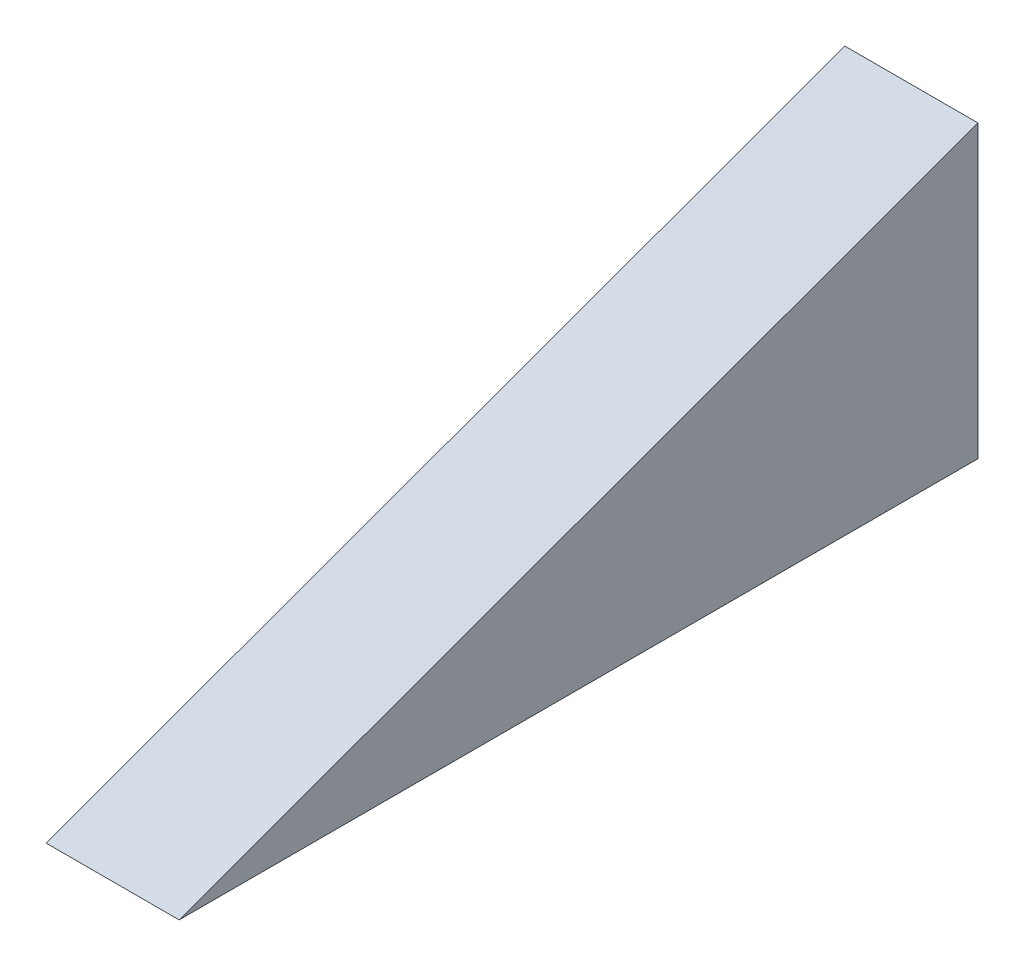
SolidWorks part; units mm, degrees
ref_plane "Front Plane" through (0, 0, 0) normal (0, 0, 1) x (1, 0, 0)
ref_plane "Top Plane" through (0, 0, 0) normal (0, 1, 0) x (1, 0, 0)
ref_plane "Right Plane" through (0, 0, 0) normal (1, 0, 0) x (0, 0, -1)
sketch "Sketch1" plane through (0, 0, 0) normal (1, 0, 0) x (0, 0, -1)
  line L0 (0, 0) -> (152.4, 0)
  line L1 (152.4, 0) -> (152.4, 55.4691)
  line L2 (152.4, 55.4691) -> (0, 0)
  dimension "D1" = 152.4
  dimension "D2" = 20
extrude "Boss-Extrude1" add sketch "Sketch1" along normal blind 25.4
